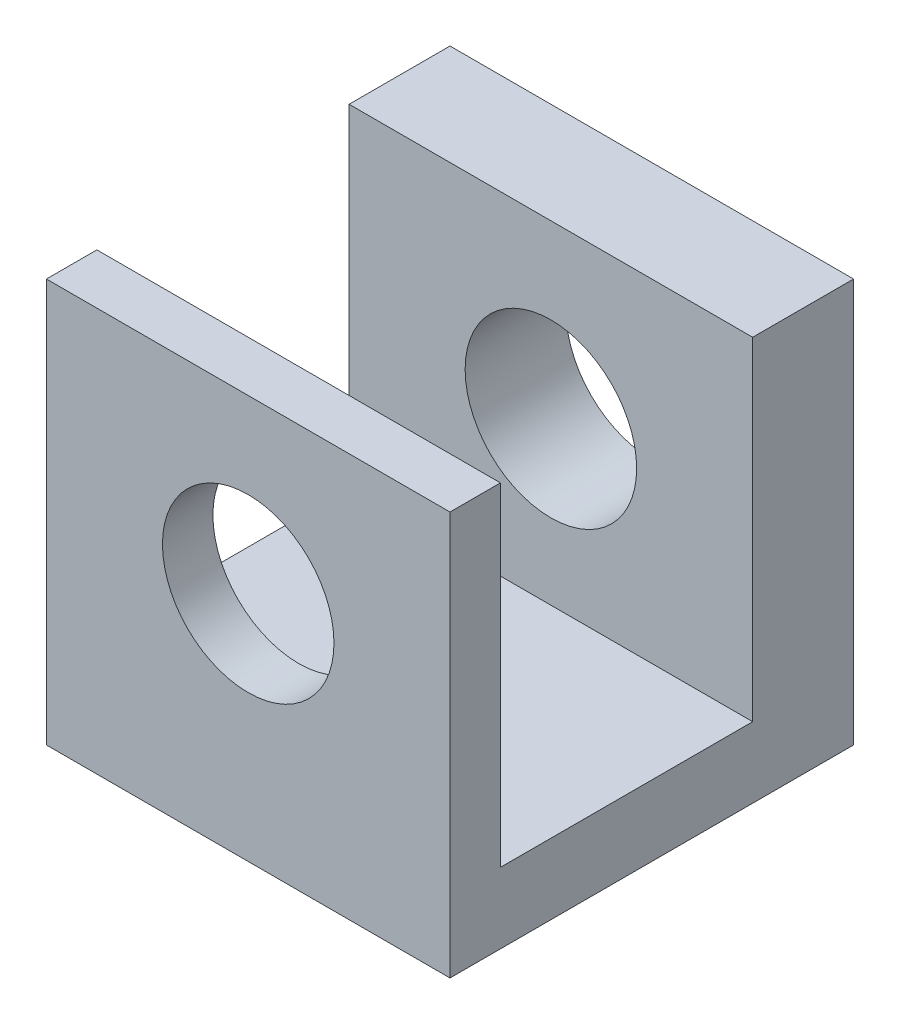
SolidWorks part; units mm, degrees
material "Plain Carbon Steel"
ref_plane "Front Plane" through (0, 0, 0) normal (0, 0, 1) x (1, 0, 0)
ref_plane "Top Plane" through (0, 0, 0) normal (0, 1, 0) x (1, 0, 0)
ref_plane "Right Plane" through (0, 0, 0) normal (1, 0, 0) x (0, 0, -1)
sketch "Sketch1" plane through (0, 0, 0) normal (0, 0, 1) x (1, 0, 0)
  line L1 (20, -20) -> (-20, -20)
  line L2 (20, -20) -> (20, 20)
  line L3 (20, 20) -> (-20, 20)
  line L4 (-20, -20) -> (-20, 20)
  line L5 (20, -20) -> (-20, 20) construction
  line L6 (20, 20) -> (-20, -20) construction
  point P0 (0, 0)
  dimension "D1" = 40
  dimension "D2" = 40
extrude "Boss-Extrude1" add sketch "Sketch1" against normal blind 40
sketch "Sketch2" plane through (20, 0, 0) normal (1, 0, 0) x (0, 0, -1)
  line L0 (40, 20) -> (0, 20) construction
  line L1 (30, -13) -> (5, -13)
  line L2 (30, -13) -> (30, 20)
  line L3 (30, 20) -> (5, 20)
  line L4 (5, -13) -> (5, 20)
  line L5 (30, -13) -> (5, 20) construction
  line L6 (30, 20) -> (5, -13) construction
  line L7 (0, -20) -> (0, 20) construction
  line L8 (40, -20) -> (40, 20) construction
  line L9 (40, -20) -> (0, -20) construction
  dimension "D1" = 5
  dimension "D2" = 10
  dimension "D3" = 7
extrude "Cut-Extrude1" cut sketch "Sketch2" against normal blind 62.5
sketch "Sketch3" plane through (0, 0, 0) normal (0, 0, 1) x (1, 0, 0)
  line L0 (0, 0) -> (0, 34.3293) construction
  circle A0 centre (0, 2.9943) radius 8.5
  dimension "D1" = 17
extrude "Cut-Extrude2" cut sketch "Sketch3" against normal blind 62.5
